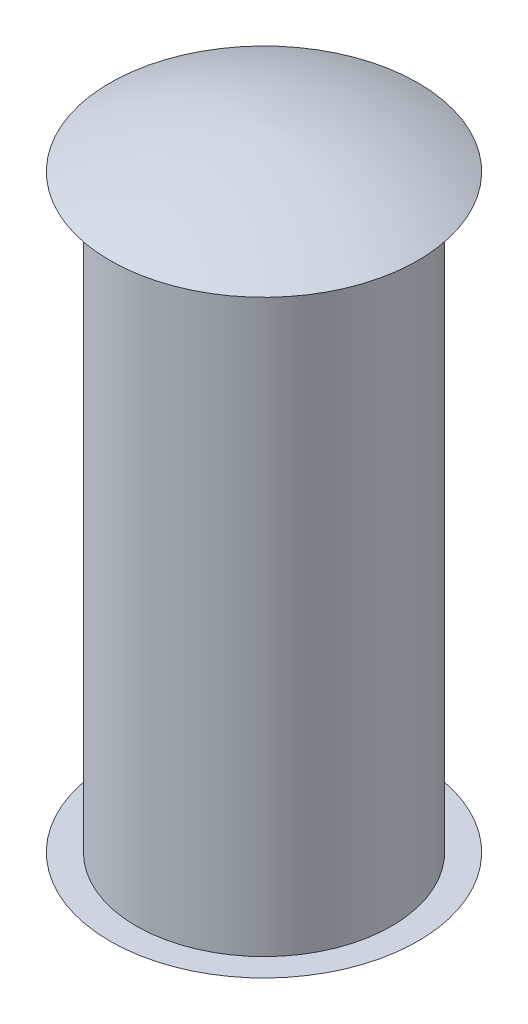
SolidWorks part; units mm, degrees
ref_plane "Front Plane" through (0, 0, 0) normal (0, 0, 1) x (1, 0, 0)
ref_plane "Top Plane" through (0, 0, 0) normal (0, 1, 0) x (1, 0, 0)
ref_plane "Right Plane" through (0, 0, 0) normal (1, 0, 0) x (0, 0, -1)
sketch "Sketch1" plane through (0, 0, 0) normal (0, 1, 0) x (1, 0, 0)
  circle A0 centre (0, 0) radius 9.75
  dimension "D1" = 19.5
extrude "Boss-Extrude1" add sketch "Sketch1" along normal blind 22.5
sketch "Sketch2" plane through (0, 0, 0) normal (0, 0, 1) x (1, 0, 0)
  line L1 (0, 22.5) -> (0, 25.5)
  line L2 (0, 22.5) -> (11.75, 22.5)
  line L3 (9.75, 22.5) -> (-9.75, 22.5) construction
  line L4 (9.75, 0) -> (9.75, 22.5) construction
  arc A0 (0, 25.5) -> (11.75, 22.5) centre (-1.3933, -4.4676) cw
  dimension "D2" = 30
  dimension "D3" = 2
  dimension "D1" = 3
revolve "Revolve1" add sketch "Sketch2" angle 360 about L1
mirror "Mirror1" about plane through (0, 0, 0) normal (0, 1, 0) of "Revolve1", "Boss-Extrude1"
